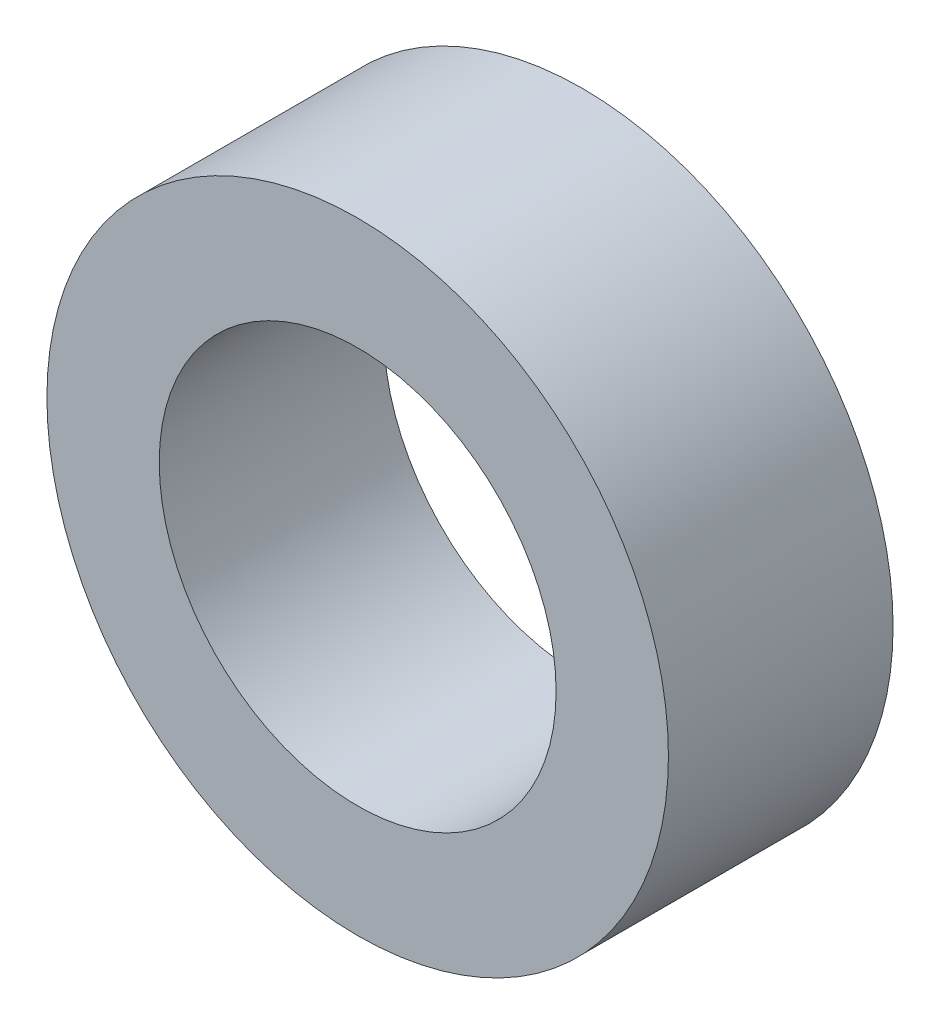
SolidWorks part; units mm, degrees
ref_plane "Front Plane" through (0, 0, 0) normal (0, 0, 1) x (1, 0, 0)
ref_plane "Top Plane" through (0, 0, 0) normal (0, 1, 0) x (1, 0, 0)
ref_plane "Right Plane" through (0, 0, 0) normal (1, 0, 0) x (0, 0, -1)
sketch "Sketch1" plane through (0, 0, 0) normal (0, 0, 1) x (1, 0, 0)
  circle A0 centre (0, 0) radius 2.65
  circle A1 centre (0, 0) radius 4.15
  dimension "D1" = 5.3
  dimension "D2" = 8.3
extrude "Boss-Extrude1" add sketch "Sketch1" along normal blind 3
